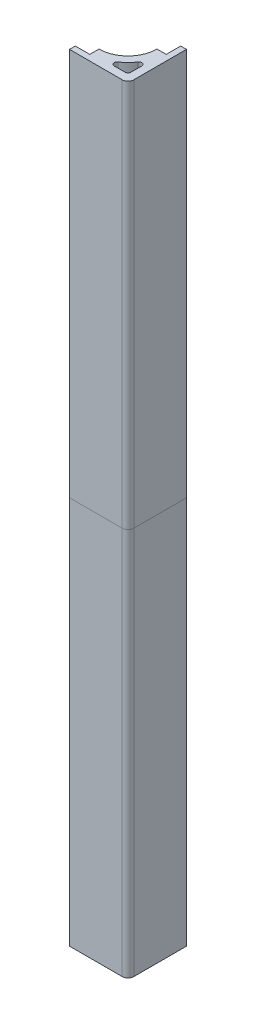
SolidWorks part; units mm, degrees
ref_plane "Front Plane" through (0, 0, 0) normal (0, 0, 1) x (1, 0, 0)
ref_plane "Top Plane" through (0, 0, 0) normal (0, 1, 0) x (1, 0, 0)
ref_plane "Right Plane" through (0, 0, 0) normal (1, 0, 0) x (0, 0, -1)
sketch "Sketch1" plane through (0, 0, 0) normal (0, 1, 0) x (1, 0, 0)
  line L6 (-5.175, 15.175) -> (-2, 15.175)
  line L7 (-15.175, 5.175) -> (-15.175, 2)
  line L8 (-15.175, 2) -> (-20.175, 2)
  line L9 (-20.175, 2) -> (-20.175, 0)
  line L10 (-20.175, 0) -> (-2, 0)
  line L11 (0, 2) -> (0, 20.175)
  line L12 (0, 20.175) -> (-2, 20.175)
  line L13 (-2, 20.175) -> (-2, 15.175)
  arc A0 (-15.175, 5.175) -> (-5.175, 15.175) centre (-15.175, 15.175) ccw
  arc A1 (-2, 0) -> (0, 2) centre (-2, 2) ccw
  point P12 (0, 0)
  dimension "D1" = 10
  dimension "D4" = 2
  dimension "D2" = 3.175
  dimension "D3" = 3.175
  dimension "D6" = 5
  dimension "D7" = 2
  dimension "D8" = 2
  dimension "D9" = 5
extrude "Boss-Extrude1" add sketch "Sketch1" along normal mid plane 267.9
shell "Shell1" thickness 2.75
fillet "Fillet1" radius 1 3 edges at (-2.75, 0, -2.75) (-12.3146, 0, -2.75) (-2.75, 0, -12.3146)
split "Split1" trim tools "Top Plane" bodies to split 101 resulting bodies 102 103
